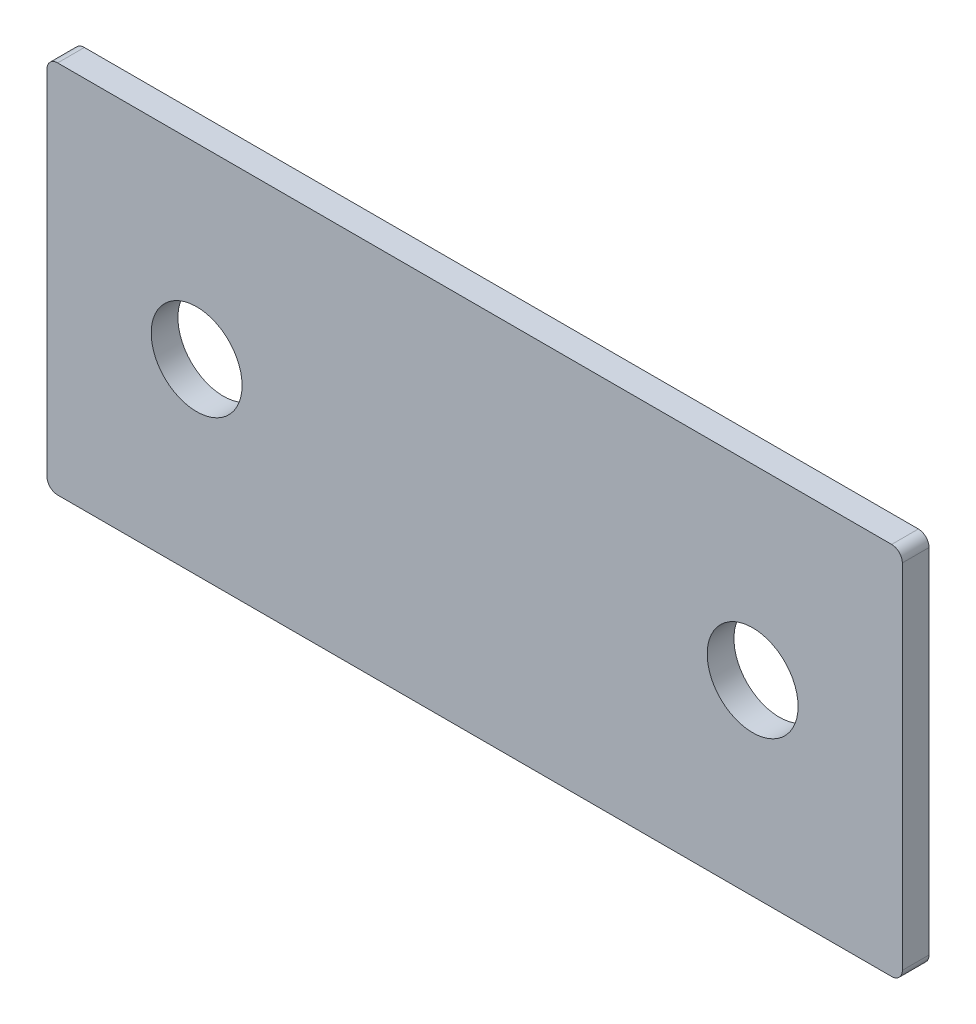
SolidWorks part; units mm, degrees
ref_plane "Спереди" through (0, 0, 0) normal (0, 0, 1) x (1, 0, 0)
ref_plane "Сверху" through (0, 0, 0) normal (0, 1, 0) x (1, 0, 0)
ref_plane "Справа" through (0, 0, 0) normal (1, 0, 0) x (0, 0, -1)
sketch "Эскиз1" plane through (0, 0, 0) normal (0, 0, 1) x (1, 0, 0)
  line L5 (-26, 0) -> (26, 0) construction
  line L6 (-40, -17.5) -> (40, -17.5)
  line L11 (-40, -17.5) -> (-40, 17.5)
  line L12 (-40, 17.5) -> (40, 17.5)
  line L16 (40, -17.5) -> (40, 17.5)
  line L17 (-40, -17.5) -> (40, 17.5) construction
  line L18 (-40, 17.5) -> (40, -17.5) construction
  circle A6 centre (-26, 0) radius 4.25
  circle A7 centre (26, 0) radius 4.25
  point P0 (0, 0)
  dimension "D4" = 8.5
  dimension "D3" = 14
  dimension "D1" = 80
  dimension "D2" = 35
extrude "Бобышка-Вытянуть1" add sketch "Эскиз1" along normal blind 2.5
fillet "Скругление1" radius 1 4 edges at (-40, -17.5, 1.25) (-40, 17.5, 1.25) (40, -17.5, 1.25) (40, 17.5, 1.25)
